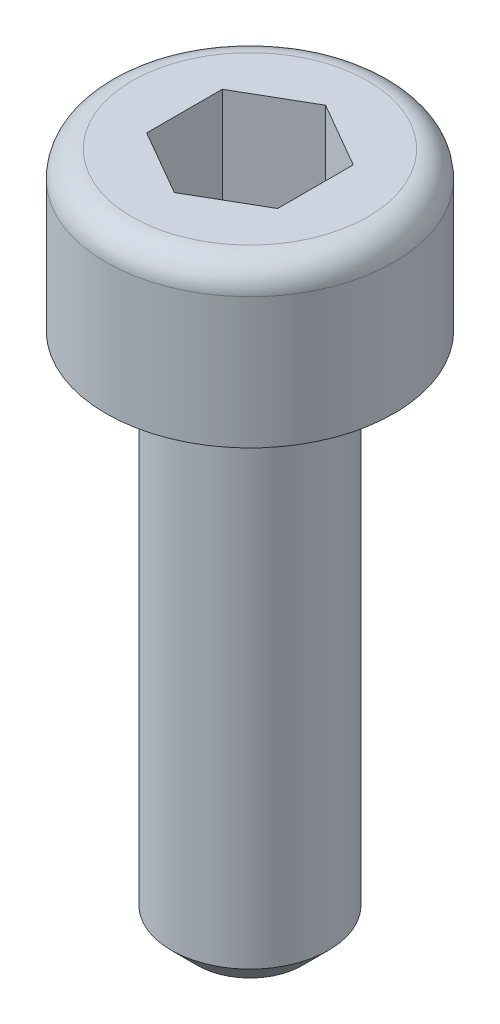
SolidWorks part; units mm, degrees
material "acero"
ref_plane "Alzado" through (0, 0, 0) normal (0, 0, 1) x (1, 0, 0)
ref_plane "Planta" through (0, 0, 0) normal (0, 1, 0) x (1, 0, 0)
ref_plane "Vista lateral" through (0, 0, 0) normal (1, 0, 0) x (0, 0, -1)
sketch "Croquis1" plane through (0, 0, 0) normal (0, 0, 1) x (1, 0, 0)
  line L0 (0, 0) -> (0, -60.9498) construction
  line L1 (0, 0) -> (2.75, 0)
  line L2 (2.75, 0) -> (2.75, -3)
  line L3 (2.75, -3) -> (1.5, -3)
  line L4 (1.5, -3) -> (1.5, -13)
  line L5 (1.5, -13) -> (0, -13)
  line L6 (0, -13) -> (0, 0)
  dimension "D1" = 10
  dimension "D2" = 3
  dimension "D3" = 5.5
  dimension "D4" = 3
revolve "Revolución1" add sketch "Croquis1" angle 360 about L0
sketch "Croquis2" plane through (0, 0, 0) normal (0, 1, 0) x (1, 0, 0)
  line L1 (1.25, 0.7217) -> (0, 1.4434)
  line L2 (0, 1.4434) -> (-1.25, 0.7217)
  line L3 (-1.25, 0.7217) -> (-1.25, -0.7217)
  line L4 (-1.25, -0.7217) -> (0, -1.4434)
  line L5 (0, -1.4434) -> (1.25, -0.7217)
  line L6 (1.25, -0.7217) -> (1.25, 0.7217)
  circle A0 centre (0, 0) radius 1.25 construction
  dimension "D1" = 2.5
extrude "Cortar-Extruir1" cut sketch "Croquis2" against normal blind 2
chamfer "Chaflán1" distance 0.5 angle 45 1 edges at (0, -13, 1.5)
fillet "Redondeo1" radius 0.5 1 edges at (0, 0, 2.75)
